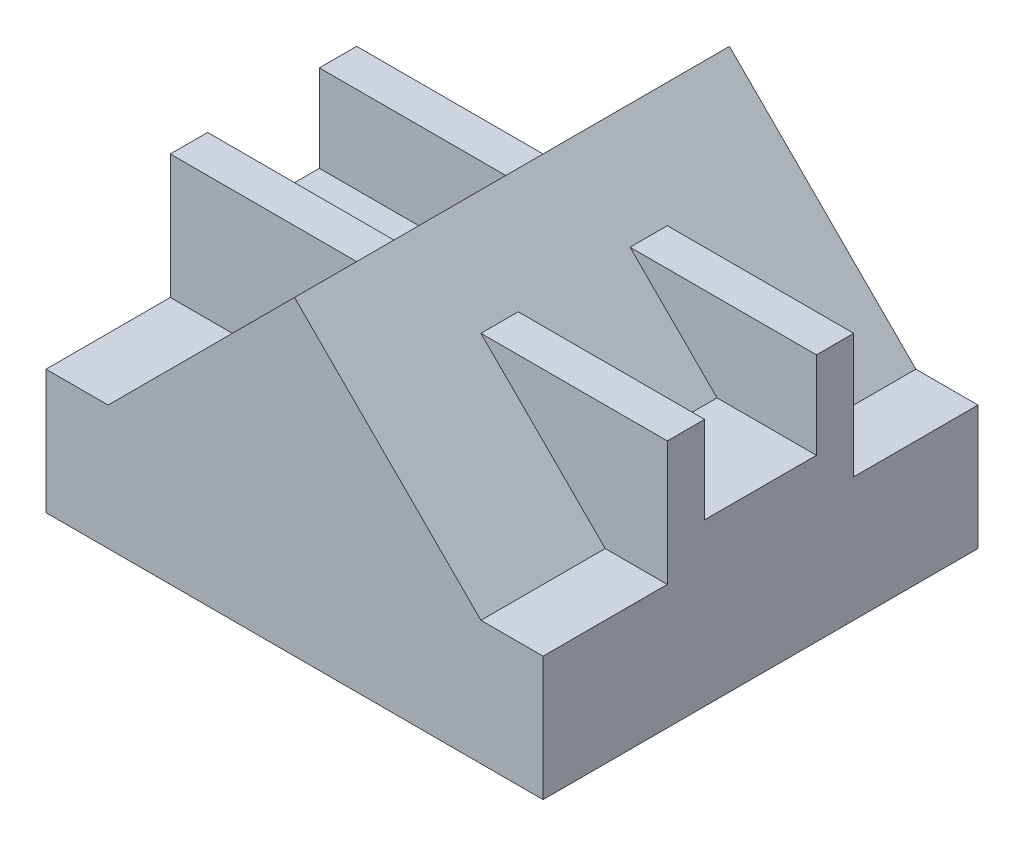
SolidWorks part; units mm, degrees
ref_plane "Front Plane" through (0, 0, 0) normal (0, 0, 1) x (1, 0, 0)
ref_plane "Top Plane" through (0, 0, 0) normal (0, 1, 0) x (1, 0, 0)
ref_plane "Right Plane" through (0, 0, 0) normal (1, 0, 0) x (0, 0, -1)
sketch "Sketch1" plane through (0, 0, 0) normal (0, 0, 1) x (1, 0, 0)
  line L0 (75, 25) -> (100, 25)
  line L1 (-100, 25) -> (-75, 25)
  line L2 (-100, 25) -> (-100, -25)
  line L3 (-100, -25) -> (100, -25)
  line L4 (100, 25) -> (100, -25)
  line L7 (0, 100) -> (-75, 25)
  line L8 (0, 100) -> (75, 25)
  point P0 (0, 0)
  dimension "D1" = 200
  dimension "D2" = 50
  dimension "D3" = 125
extrude "Boss-Extrude1" add sketch "Sketch1" along normal blind 175
sketch "Sketch2" plane through (100, 0, 0) normal (1, 0, 0) x (0, 0, -1)
  line L1 (-175, 25) -> (0, 25) construction
  line L2 (-125, 25) -> (-125, 75)
  line L3 (-125, 75) -> (-110, 75)
  line L4 (-110, 75) -> (-110, 40)
  line L5 (-110, 40) -> (-65, 40)
  line L6 (-65, 40) -> (-65, 75)
  line L7 (-65, 75) -> (-50, 75)
  line L8 (-50, 75) -> (-50, 25)
  line L11 (-125, 25) -> (-50, 25)
  dimension "D1" = 50
  dimension "D2" = 100
  dimension "D3" = 100
  dimension "D4" = 15
  dimension "D5" = 15
  dimension "D6" = 15
extrude "Boss-Extrude2" add sketch "Sketch2" against normal blind 200
